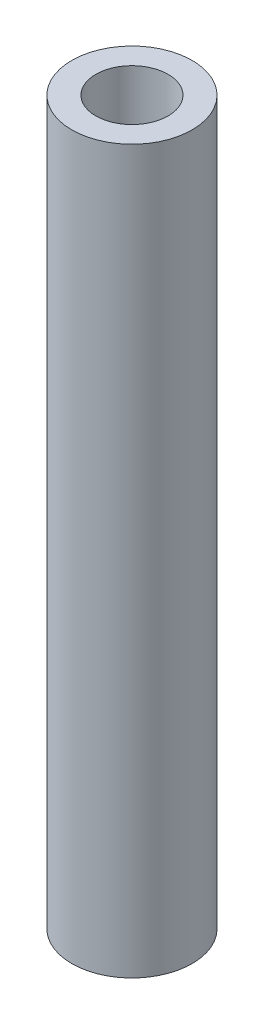
SolidWorks part; units mm, degrees
material "6061 合金"
ref_plane "前视基准面" through (0, 0, 0) normal (0, 0, 1) x (1, 0, 0)
ref_plane "上视基准面" through (0, 0, 0) normal (0, 1, 0) x (1, 0, 0)
ref_plane "右视基准面" through (0, 0, 0) normal (1, 0, 0) x (0, 0, -1)
sketch "草图1" plane through (0, 0, 0) normal (0, 1, 0) x (1, 0, 0)
  circle A0 centre (0, 0) radius 2.5
  circle A1 centre (0, 0) radius 1.5
extrude "凸台-拉伸1" add sketch "草图1" along normal blind 30
